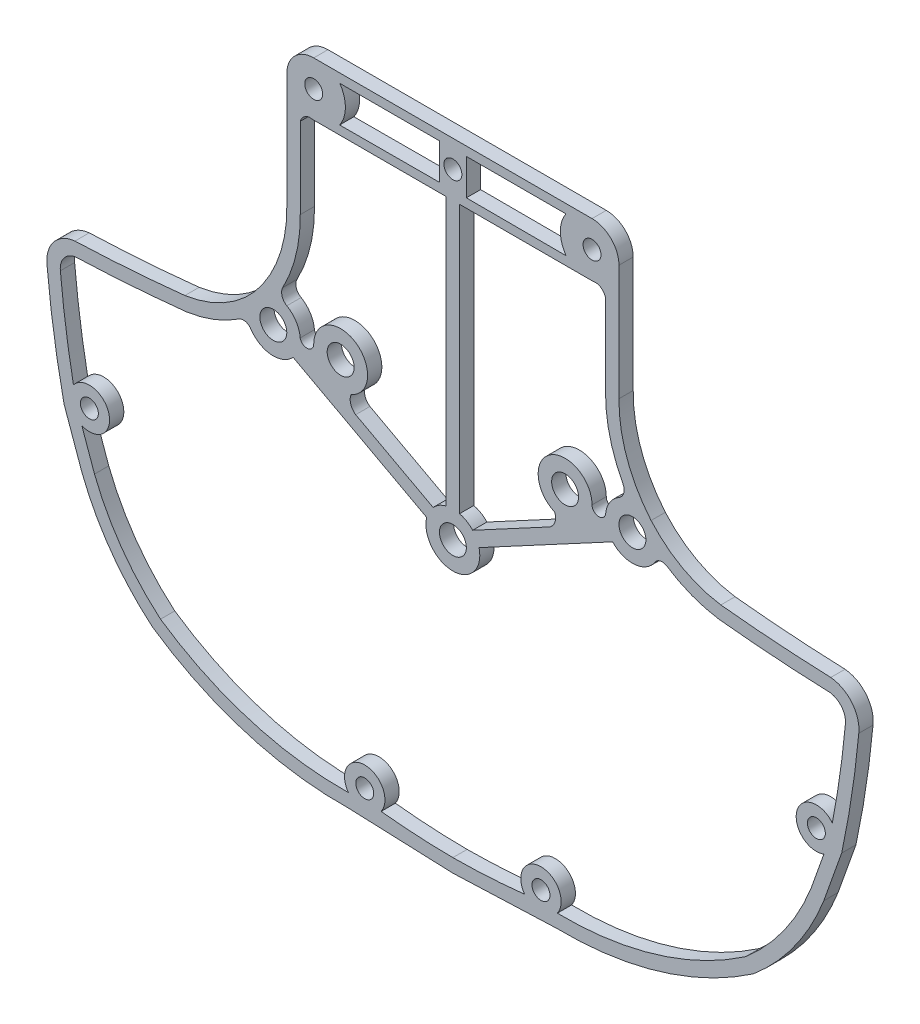
SolidWorks part; units mm, degrees
ref_plane "Front Plane" through (0, 0, 0) normal (0, 0, 1) x (1, 0, 0)
ref_plane "Top Plane" through (0, 0, 0) normal (0, 1, 0) x (1, 0, 0)
ref_plane "Right Plane" through (0, 0, 0) normal (1, 0, 0) x (0, 0, -1)
sketch "Sketch4" plane through (0, 0, 0) normal (0, 0, 1) x (1, 0, 0)
  line L0 (0, -3) -> (0, 1.5) construction
  line L1 (-41.3263, -9.6459) -> (-39.9169, -13.6055)
  line L2 (-11.6104, -31.6846) -> (0, -32.1446)
  line L3 (-15.5, 38.75) -> (15.5, 38.75)
  line L4 (-18.5, 35.75) -> (-18.5, 22.8725)
  line L5 (-17, 22.8813) -> (-17, 31.8851)
  line L6 (-43.3103, -8.5451) -> (-41.3154, -14.148)
  line L7 (43.3103, -8.5451) -> (41.3154, -14.148)
  line L8 (-15.5, 32.75) -> (-0.75, 32.75)
  line L9 (-41.3263, -9.6459) -> (-39.9169, -13.6055)
  line L10 (1.5, 37.75) -> (1.5, 33.75)
  line L11 (17, 22.8813) -> (17, 31.8851)
  line L12 (18.5, 35.75) -> (18.5, 22.8725)
  line L13 (11.6104, -31.6846) -> (0, -32.1446)
  line L14 (0, -32.1446) -> (0, -30.6446) construction
  line L15 (41.3263, -9.6459) -> (39.9169, -13.6055)
  line L16 (0, -28.8663) -> (0, 11.1337) construction
  line L17 (1.5, 33.75) -> (12.6125, 33.7217)
  line L18 (-1.5, 37.75) -> (-12.5929, 37.75)
  line L19 (-1.5, 33.75) -> (-12.6125, 33.7217)
  line L20 (-1.5, 37.75) -> (-1.5, 33.75)
  line L21 (0, 11.1337) -> (-12.5, 11.1337) construction
  line L22 (1.5, 37.75) -> (12.5929, 37.75)
  line L23 (2.9136, 0.7146) -> (17.7965, 8.7142)
  line L24 (0, 11.1337) -> (12.5, 11.1337) construction
  line L25 (2.2035, 2.0358) -> (10.8242, 6.6695)
  line L26 (-2.2035, 2.0358) -> (-10.8242, 6.6695)
  line L27 (-43.3103, -8.5451) -> (-41.3154, -14.148)
  line L28 (-2.9136, 0.7146) -> (-17.7965, 8.7142)
  line L29 (-0.75, 32.75) -> (-0.75, 2.9047)
  line L30 (0.75, 32.75) -> (0.75, 2.9047)
  line L33 (0.75, 32.75) -> (15.5, 32.75)
  circle A0 centre (-16.9277, -13.0525) radius 0.75 construction
  circle A1 centre (-12.5, 11.1337) radius 1.5
  circle A2 centre (-20, 10.75) radius 1.5
  arc A3 (18.953, 14.8653) -> (17, 22.8813) centre (33.6375, 22.6888) cw
  circle A4 centre (-15.5, 35.75) radius 1
  arc A5 (-41.3154, -14.148) -> (-33.4728, -25.1215) centre (-15.9458, -4.3058) ccw
  arc A6 (-41.3263, -9.6459) -> (-42.2626, -6.1729) centre (-40.489, -7.5575) ccw
  arc A7 (-0.75, 2.9047) -> (-2.2035, 2.0358) centre (0, 0) ccw
  circle A8 centre (-9.8152, -28.8663) radius 1
  arc A9 (-39.9169, -13.6055) -> (-32.5625, -23.9268) centre (-15.9458, -4.3058) ccw
  arc A10 (-7.992, -30.1848) -> (-11.6383, -30.1848) centre (-9.8152, -28.8663) ccw
  arc A11 (-11.6383, -30.1848) -> (-32.5625, -23.9268) centre (-12.3075, 5.6876) cw
  arc A12 (15.5, 32.75) -> (15.955, 32.7847) centre (15.5, 35.75) ccw
  arc A13 (-15.955, 32.7847) -> (-15.5, 32.75) centre (-15.5, 35.75) ccw
  circle A14 centre (0, 0) radius 1.5
  arc A15 (-2.9136, 0.7146) -> (2.9136, 0.7146) centre (0, 0) ccw
  arc A16 (-11.6104, -31.6846) -> (-33.4728, -25.1215) centre (-12.3075, 5.6876) cw
  arc A17 (-11.5539, -27.4383) -> (-7.7996, -29.8663) centre (-9.8152, -28.8663) ccw construction
  arc A18 (39.9169, -13.6055) -> (32.5625, -23.9268) centre (15.9458, -4.3058) cw
  circle A19 centre (0, 35.75) radius 1
  arc A20 (-22.5154, 9.1152) -> (-17.7965, 8.7142) centre (-20, 10.75) ccw
  arc A21 (17, 31.8851) -> (15.955, 32.7847) centre (15.8188, 31.5698) ccw
  arc A22 (-43.3103, -8.5451) -> (-45.2127, 3.9531) centre (59.9942, 13.5734) cw
  arc A23 (-43.7203, 4.1043) -> (-41.989, 6.285) centre (-41.7643, 4.329) cw
  arc A24 (-7.992, -30.1848) -> (0, -30.6446) centre (0.4684, 47.1878) ccw
  arc A25 (-15.5, 38.75) -> (-18.5, 35.75) centre (-15.5, 35.75) ccw
  arc A26 (-18.953, 14.8653) -> (-18.4928, 13.3439) centre (-17.9197, 14.3475) ccw
  circle A27 centre (40.489, -7.5575) radius 1
  arc A28 (29.658, 7.1648) -> (23.8472, 9.3846) centre (31.7248, 21.2913) cw
  arc A29 (41.989, 6.285) -> (29.658, 7.1648) centre (48.4717, 183.9785) cw
  arc A30 (43.7203, 4.1043) -> (41.989, 6.285) centre (41.7643, 4.329) ccw
  arc A31 (42.2626, -6.1729) -> (43.7203, 4.1043) centre (-59.9942, 13.5734) ccw
  arc A32 (7.992, -30.1848) -> (0, -30.6446) centre (-0.4684, 47.1878) cw
  arc A33 (22.0771, 12.9146) -> (18.5, 22.8725) centre (33.6375, 22.6888) cw
  arc A34 (23.8472, 9.3846) -> (22.5154, 9.1151) centre (23.316, 8.584) ccw
  arc A35 (18.5, 35.75) -> (15.5, 38.75) centre (15.5, 35.75) ccw
  arc A36 (-45.2127, 3.9531) -> (-42.0937, 7.7821) centre (-41.7643, 4.329) cw
  circle A37 centre (-40.489, -7.5575) radius 1
  arc A38 (29.8468, 8.6532) -> (22.0771, 12.9146) centre (31.7248, 21.2913) cw
  arc A39 (42.0937, 7.7821) -> (29.8468, 8.6532) centre (48.4717, 183.9785) cw
  arc A40 (45.2127, 3.9531) -> (42.0937, 7.7821) centre (41.7643, 4.329) ccw
  arc A41 (11.6104, -31.6846) -> (33.4728, -25.1215) centre (12.3075, 5.6876) ccw
  arc A42 (42.2626, -6.1729) -> (41.3263, -9.6459) centre (40.489, -7.5575) ccw
  arc A43 (-42.0937, 7.7821) -> (-29.8468, 8.6532) centre (-48.4717, 183.9785) ccw
  arc A44 (-29.8468, 8.6532) -> (-22.0771, 12.9146) centre (-31.7248, 21.2913) ccw
  arc A45 (-43.3103, -8.5451) -> (-45.2127, 3.9531) centre (59.9942, 13.5734) cw
  arc A46 (-23.8472, 9.3846) -> (-22.5154, 9.1152) centre (-23.316, 8.584) cw
  arc A47 (-22.0771, 12.9146) -> (-18.5, 22.8725) centre (-33.6375, 22.6888) ccw
  arc A48 (11.6383, -30.1848) -> (32.5625, -23.9268) centre (12.3075, 5.6876) ccw
  arc A49 (-42.2626, -6.1729) -> (-43.7203, 4.1043) centre (59.9942, 13.5734) cw
  arc A50 (7.992, -30.1848) -> (11.6383, -30.1848) centre (9.8152, -28.8663) cw
  arc A51 (-41.989, 6.285) -> (-29.658, 7.1648) centre (-48.4717, 183.9785) ccw
  arc A52 (-29.658, 7.1648) -> (-23.8472, 9.3846) centre (-31.7248, 21.2913) ccw
  circle A53 centre (9.8152, -28.8663) radius 1
  arc A54 (41.3154, -14.148) -> (33.4728, -25.1215) centre (15.9458, -4.3058) cw
  arc A55 (-17, 31.8851) -> (-15.955, 32.7847) centre (-15.8188, 31.5698) cw
  circle A56 centre (12.5, 11.1337) radius 1.5
  arc A57 (-17.0087, 10.9788) -> (-18.5037, 13.3502) centre (-20, 10.75) ccw
  arc A58 (18.953, 14.8653) -> (18.4928, 13.3439) centre (17.9197, 14.3475) cw
  arc A59 (-11.223, 8.4191) -> (-15.5, 11.1337) centre (-12.5, 11.1337) ccw
  arc A60 (15.5, 11.1337) -> (11.223, 8.4191) centre (12.5, 11.1337) ccw
  arc A61 (-15.5, 11.1337) -> (-17.0087, 10.9788) centre (-16.2623, 11.1337) cw
  arc A62 (-11.3833, 8.2316) -> (-10.8242, 6.6695) centre (-10.0267, 7.836) ccw
  arc A63 (-11.3833, 8.2316) -> (-11.223, 8.4191) centre (-11.0953, 8.1476) cw
  arc A64 (11.3833, 8.2316) -> (11.223, 8.4191) centre (11.0953, 8.1476) ccw
  arc A65 (43.3103, -8.5451) -> (45.2127, 3.9531) centre (-59.9942, 13.5734) ccw
  arc A66 (22.5154, 9.1151) -> (17.7965, 8.7142) centre (20, 10.75) cw
  arc A67 (11.3833, 8.2316) -> (10.8242, 6.6695) centre (10.0267, 7.836) cw
  arc A68 (15.5, 11.1337) -> (17.0087, 10.9788) centre (16.2623, 11.1337) ccw
  circle A72 centre (15.5, 35.75) radius 1
  circle A73 centre (20, 10.75) radius 1.5
  arc A74 (-18.953, 14.8653) -> (-17, 22.8813) centre (-33.6375, 22.6888) ccw
  arc A75 (-12.5929, 37.75) -> (-12.6125, 33.7217) centre (-15.5, 35.75) cw
  arc A77 (12.5929, 37.75) -> (12.6125, 33.7217) centre (15.5, 35.75) ccw
  arc A78 (2.2035, 2.0358) -> (0.75, 2.9047) centre (0, 0) ccw
  arc A79 (17.0087, 10.9788) -> (18.5037, 13.3502) centre (20, 10.75) cw
  point P16 (0, -7.5575)
  point P44 (0, 8.1)
  point P114 (0, 37.9632)
  dimension "D1" = 0.3
  dimension "D3" = 1.5
extrude "Boss-Extrude2" add sketch "Sketch4" along normal blind 1.5875
sketch "Sketch5" plane through (0, 0, 1.5875) normal (0, 0, 1) x (1, 0, 0)
